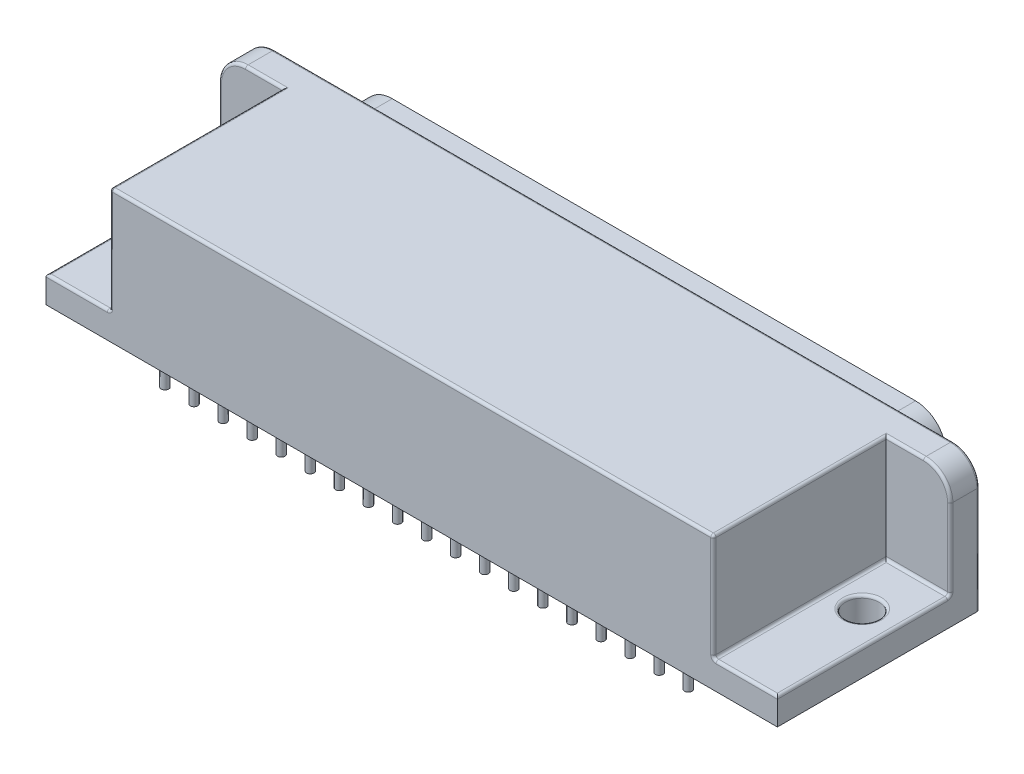
SolidWorks part; units mm, degrees
ref_plane "x/y" through (0, 0, 0) normal (0, 0, 1) x (1, 0, 0)
ref_plane "x/z" through (0, 0, 0) normal (0, 1, 0) x (1, 0, 0)
ref_plane "y/z" through (0, 0, 0) normal (1, 0, 0) x (0, 0, -1)
sketch "Sketch1" plane through (0, 0, 0) normal (0, 1, 0) x (1, 0, 0)
  line L1 (-9.906, -1.4224) -> (59.7408, -1.4224)
  line L2 (-9.906, -1.4224) -> (-9.906, 17.8308)
  line L3 (-9.906, 17.8308) -> (59.7408, 17.8308)
  line L4 (59.7408, -1.4224) -> (59.7408, 17.8308)
  point P3 (24.9174, 17.8308)
  dimension "D1" = 69.6468
  dimension "D2" = 19.2532
  dimension "D3" = 1.4224
  dimension "D4" = 9.906
extrude "Base-Extrude" add sketch "Sketch1" along normal blind 12.7
sketch "Sketch2" plane through (0, 0, -17.8308) normal (0, 0, -1) x (-1, 0, 0)
  line L0 (-24.9174, 12.7) -> (-24.9174, -6.5379) construction
  line L1 (-59.7408, 12.7) -> (9.906, 12.7) construction
  line L2 (-49.3393, 2.032) -> (-0.4955, 2.032)
  line L3 (2.3614, 4.3892) -> (2.8571, 6.9513)
  line L4 (0.0002, 10.414) -> (-49.835, 10.414)
  line L5 (-59.7408, 0) -> (9.906, 0) construction
  line L6 (-52.1962, 4.3892) -> (-52.6919, 6.9513)
  arc A0 (2.3614, 4.3892) -> (-0.4955, 2.032) centre (-0.4955, 4.9419) cw
  arc A1 (0.0002, 10.414) -> (2.8571, 6.9513) centre (0.0002, 7.5041) cw
  arc A2 (-49.835, 10.414) -> (-52.6919, 6.9513) centre (-49.835, 7.5041) ccw
  arc A3 (-52.1962, 4.3892) -> (-49.3393, 2.032) centre (-49.3393, 4.9419) ccw
  point P4 (-24.9174, 10.414)
  point P12 (1.9054, 2.032)
  point P21 (-24.9174, 2.032)
  dimension "D1" = 2.032
  dimension "D2" = 8.382
  dimension "D3" = 100.95
  dimension "D4" = 48.8437
  dimension "D6" = 49.8351
extrude "Boss-Extrude1" add sketch "Sketch2" along normal blind 3.81
sketch "Sketch13" plane through (0, 0, -21.6408) normal (0, 0, -1) x (-1, 0, 0)
  line L8 (2.112, 4.4374) -> (2.6077, 6.9996)
  line L9 (0.0002, 10.16) -> (-49.835, 10.16)
  line L10 (-52.4425, 6.9996) -> (-51.9468, 4.4374)
  line L11 (-49.3393, 2.286) -> (-0.4955, 2.286)
  line L12 (2.112, 4.4374) -> (2.6077, 6.9996)
  line L13 (0.0002, 10.16) -> (-49.835, 10.16)
  line L14 (-52.4425, 6.9996) -> (-51.9468, 4.4374)
  line L15 (-49.3393, 2.286) -> (-0.4955, 2.286)
  arc A8 (-0.4955, 2.286) -> (2.112, 4.4374) centre (-0.4955, 4.9419) ccw
  arc A9 (2.6077, 6.9996) -> (0.0002, 10.16) centre (0.0002, 7.5041) ccw
  arc A10 (-49.835, 10.16) -> (-52.4425, 6.9996) centre (-49.835, 7.5041) ccw
  arc A11 (-51.9468, 4.4374) -> (-49.3393, 2.286) centre (-49.3393, 4.9419) ccw
  arc A12 (-0.4955, 2.286) -> (2.112, 4.4374) centre (-0.4955, 4.9419) ccw
  arc A13 (2.6077, 6.9996) -> (0.0002, 10.16) centre (0.0002, 7.5041) ccw
  arc A14 (-49.835, 10.16) -> (-52.4425, 6.9996) centre (-49.835, 7.5041) ccw
  arc A15 (-51.9468, 4.4374) -> (-49.3393, 2.286) centre (-49.3393, 4.9419) ccw
  dimension "D1" = 0.254
extrude "Cut-Extrude5" cut sketch "Sketch13" against normal blind 3.81
sketch "Sketch4" plane through (0, 0, -17.8308) normal (0, 0, -1) x (-1, 0, 0)
  line L0 (9.906, 12.7) -> (9.906, 0) construction
  line L2 (-59.7408, 12.7) -> (9.906, 12.7) construction
  circle A0 centre (-0.254, 7.62) radius 0.508
  dimension "D1" = 1.016
  dimension "D2" = 10.16
  dimension "D3" = 5.08
extrude "Boss-Extrude4" add sketch "Sketch4" along normal blind 3.81
fillet "Fillet7" radius 0.4826 1 edges at (-0.254, 7.62, -21.6408)
pattern_linear "LPattern5" count 19 spacing 2.7686 along (1, 0, 0) of "Boss-Extrude4", "Fillet7"
sketch "Sketch5" plane through (0, 0, -17.8308) normal (0, 0, -1) x (-1, 0, 0)
  line L0 (9.906, 12.7) -> (9.906, 0) construction
  line L2 (-59.7408, 0) -> (9.906, 0) construction
  circle A0 centre (-1.651, 5.08) radius 0.508
  circle A2 centre (-0.254, 7.62) radius 0.508 construction
  dimension "D2" = 5.08
  dimension "D1" = 11.557
extrude "Boss-Extrude6" add sketch "Sketch5" along normal blind 3.81
fillet "Fillet8" radius 0.4826 1 edges at (1.143, 5.08, -21.6408)
pattern_linear "LPattern6" count 18 spacing 2.7686 along (1, 0, 0) of "Fillet8", "Boss-Extrude6"
sketch "Sketch6" plane through (0, 0, 0) normal (0, -1, 0) x (1, 0, 0)
  circle A0 centre (0, 0) radius 0.3556
  dimension "D1" = 0.7112
extrude "Boss-Extrude2" add sketch "Sketch6" along normal blind 2.54
pattern_linear "LPattern1" count 19 spacing 2.7686 along (1, 0, 0) of "Boss-Extrude2"
sketch "Sketch7" plane through (0, 0, 0) normal (0, -1, 0) x (1, 0, 0)
  line L1 (-9.906, -17.8308) -> (-9.906, 1.4224) construction
  circle A0 centre (1.651, -2.54) radius 0.3556
  dimension "D1" = 0.7112
  dimension "D2" = 11.557
  dimension "D3" = 2.54
extrude "Boss-Extrude3" add sketch "Sketch7" along normal up to surface (2.54 mm away) up to face at (0, -2.54, -0.3556)
pattern_linear "LPattern4" count 18 spacing 2.7686 along (1, 0, 0) of "Boss-Extrude3"
ref_plane "Plane1" through (24.9174, 0, 0) normal (1, 0, 0) x (0, 0, -1)
sketch "Sketch9" plane through (0, 0, 1.4224) normal (0, 0, 1) x (1, 0, 0)
  line L1 (-9.906, 12.7) -> (-3.81, 12.7)
  line L2 (-9.906, 12.7) -> (-9.906, 2.54)
  line L3 (-9.906, 2.54) -> (-3.81, 2.54)
  line L4 (-3.81, 12.7) -> (-3.81, 2.54)
  dimension "D1" = 10.16
  dimension "D2" = 6.096
extrude "Cut-Extrude3" cut sketch "Sketch9" against normal blind 16.4592
sketch "Sketch11" plane through (0, 2.54, 0) normal (0, 1, 0) x (-1, 0, 0)
  line L0 (9.906, 1.4224) -> (3.81, 1.4224) construction
  line L1 (9.906, -15.0368) -> (9.906, 1.4224) construction
  circle A0 centre (6.731, -9.8298) radius 1.5875
  point P2 (6.858, 1.4224)
  dimension "D1" = 3.175
  dimension "D2" = 11.2522
  dimension "D3" = 3.175
extrude "Cut-Extrude4" cut sketch "Sketch11" against normal through all
mirror "Mirror1" about plane through (24.9174, 0, 0) normal (1, 0, 0) of "Cut-Extrude4", "Cut-Extrude3"
fillet "Fillet1" radius 2.54 2 edges at (-9.906, 12.7, -16.4338) (59.7408, 7.62, -15.0368)
fillet "Fillet2" radius 0.254 26 edges at (24.9174, 12.7, 1.4224) (-9.906, 2.54, -6.8072) (-5.588, 12.7, -15.0368) (-3.81, 12.7, -6.8072) (-6.858, 2.54, -15.0368) (-3.81, 2.54, -6.8072) (-6.858, 2.54, 1.4224) (-3.81, 7.62, 1.4224) (-6.731, 2.54, -8.2423) (56.6928, 2.54, 1.4224) (59.7408, 2.54, -6.8072) (53.6448, 7.62, 1.4224) (53.6448, 2.54, -6.8072) (53.6448, 12.7, -6.8072) (56.6928, 2.54, -15.0368) (55.4228, 12.7, -15.0368) (56.5658, 2.54, -8.2423) (24.9174, 12.7, -17.8308) (-9.906, 6.35, -15.0368) (-9.1621, 11.9561, -15.0368) (-9.906, 5.08, -17.8308) (59.7408, 5.08, -17.8308) (58.9969, 11.9561, -17.8308) (-9.1621, 11.9561, -17.8308) (59.7408, 6.35, -15.0368) (58.9969, 11.9561, -15.0368)
